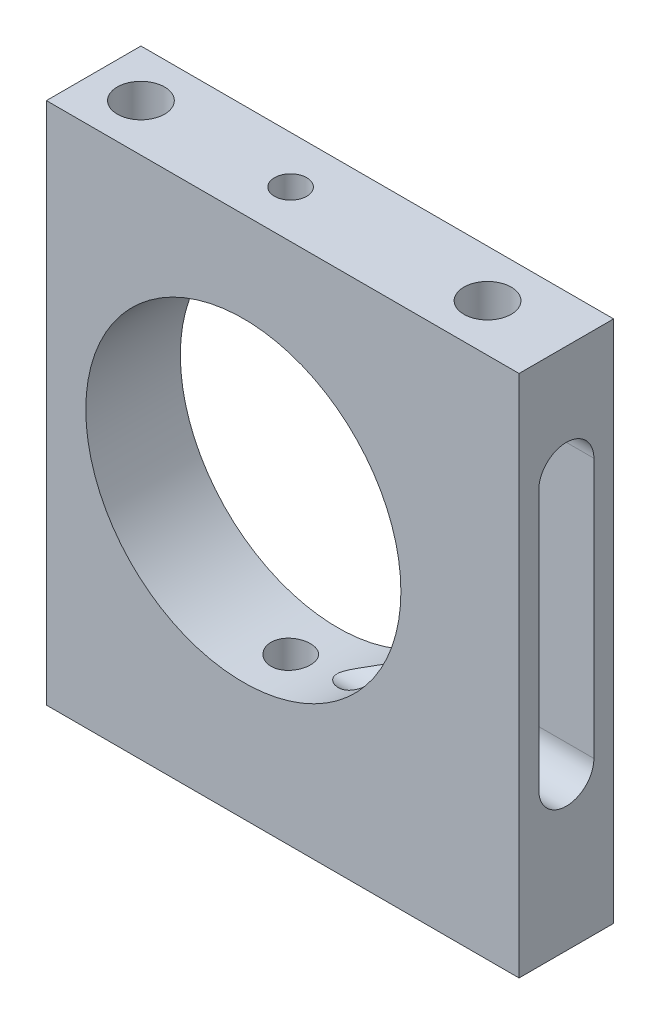
SolidWorks part; units mm, degrees
material "6061-T6 (SS)"
ref_plane "Front Plane" through (0, 0, 0) normal (0, 0, 1) x (1, 0, 0)
ref_plane "Top Plane" through (0, 0, 0) normal (0, 1, 0) x (1, 0, 0)
ref_plane "Right Plane" through (0, 0, 0) normal (1, 0, 0) x (0, 0, -1)
sketch "Sketch1" plane through (0, 0, 0) normal (0, 0, 1) x (1, 0, 0)
  line L1 (-17.5, -17.5) -> (17.5, -17.5)
  line L2 (-17.5, -17.5) -> (-17.5, 15.73)
  line L3 (-17.5, 15.73) -> (17.5, 15.73)
  line L4 (17.5, -17.5) -> (17.5, 15.73)
  line L5 (-17.5, -17.5) -> (0, 0) construction
  line L6 (0, 0) -> (17.5, -17.5) construction
  circle A0 centre (0, 0) radius 10
  point P0 (0, 0)
  dimension "D3" = 20
  dimension "D1" = 35
  dimension "D2" = 15.73
  dimension "D4" = 17.5
extrude "Boss-Extrude1" add sketch "Sketch1" along normal blind 6
sketch "Sketch2" plane through (17.5, 0, 0) normal (1, 0, 0) x (0, 0, -1)
  line L0 (-3, 15.73) -> (-3, -16.6121) construction
  line L1 (-6, 15.73) -> (0, 15.73) construction
  line L2 (-6.0882, -0.4411) -> (0.0882, -0.4411) construction
  line L5 (-4.75, -7.8061) -> (-4.75, 8.6939)
  line L7 (-1.25, -7.8061) -> (-1.25, 8.6939)
  arc A0 (-1.25, 8.6939) -> (-4.75, 8.6939) centre (-3, 8.6939) ccw
  arc A1 (-4.75, -7.8061) -> (-1.25, -7.8061) centre (-3, -7.8061) ccw
  point P6 (-3, -0.4411)
  point P12 (-3, -0.4411)
  dimension "D4" = 1.75
  dimension "D3" = 3.5
extrude "Cut-Extrude1" cut sketch "Sketch2" against normal blind 16
sketch "Sketch3" plane through (0, -17.5, 0) normal (0, -1, 0) x (1, 0, 0)
  line L0 (0, 4.6396) -> (0, 2.8092) construction
  line L1 (-2.1194, 3) -> (1.9267, 3) construction
  line L2 (17.5, 0) -> (-17.5, 0) construction
  dimension "D1" = 3
sketch "Sketch6" plane through (0, 15.73, 0) normal (0, 1, 0) x (1, 0, 0)
  line L0 (-14.9319, -3) -> (14.8838, -3) construction
  line L1 (-9.5, -2.1937) -> (-9.5, -5.6136) construction
  line L2 (12.5, -2.5791) -> (12.5, -5.6136) construction
  line L4 (17.5, -6) -> (17.5, 0) construction
  line L5 (17.5, 0) -> (-17.5, 0) construction
  dimension "D1" = 3
  dimension "D2" = 5
  dimension "D3" = 22
hole_wizard "Ø3.0mm Dowel Hole1" positions "Sketch7" profile "Sketch8" hole size "Ø3.0" standard "ANSI Metric"
sketch "Sketch7" plane through (0, 15.73, 0) normal (0, 1, 0) x (1, 0, 0)
  line L0 (-14.9319, -3) -> (14.8838, -3) construction
  line L1 (-9.5, -2.1937) -> (-9.5, -5.6136) construction
  line L2 (12.5, -2.5791) -> (12.5, -5.6136) construction
  point P0 (-9.5, -3)
  point P6 (12.5, -3)
sketch "Sketch8" plane through (-9.5, 15.73, 3) normal (1, 0, 0) x (0, 0, 1)
  line L0 (0, 0) -> (0, 8.1013)
  line L1 (0, 8.1013) -> (1.5, 7.2)
  line L2 (1.5, 7.2) -> (1.5, 0)
  line L5 (1.5, 0) -> (0, 0)
  line L10 (0, 8.1013) -> (-1.5, 7.2) construction
  line L11 (0, -6.35) -> (0, 107.95) construction
  dimension "Hole Dia." = 3
  dimension "Hole Depth" = 7.2
  dimension "Drill Angle" = 118
sketch "Sketch9" plane through (-17.5, 0, 0) normal (-1, 0, 0) x (0, 0, 1)
  line L1 (6, 15.73) -> (0, 15.73)
  line L2 (6, 15.73) -> (6, -17.5)
  line L3 (6, -17.5) -> (0, -17.5)
  line L4 (0, 15.73) -> (0, -17.5)
  line L5 (6, 15.73) -> (0, -17.5) construction
  line L6 (6, -17.5) -> (0, 15.73) construction
  point P4 (3, -0.885)
extrude "Cut-Extrude2" cut sketch "Sketch9" against normal blind 5
hole_wizard "M2.5x0.45 Tapped Hole1" positions "Sketch10" profile "Sketch11" tap size "M2.5x0.45" standard "ANSI Metric"
sketch "Sketch10" plane through (0, 15.73, 0) normal (0, 1, 0) x (1, 0, 0)
  line L0 (0, -4.6396) -> (0, -2.8092) construction
  line L1 (-2.1194, -3) -> (1.9267, -3) construction
  point P0 (0, -3)
sketch "Sketch11" plane through (0, 15.73, 3) normal (1, 0, 0) x (0, 0, 1)
  line L0 (0, 0) -> (0, 5.73)
  line L1 (0, 5.73) -> (1.025, 5.73)
  line L2 (1.025, 5.73) -> (1.025, 0)
  line L5 (1.025, 0) -> (0, 0)
  line L11 (0, -6.35) -> (0, 107.95) construction
  dimension "Thru Tap Drill Dia." = 2.05
  dimension "Thru Tap Drill Depth" = 5.73
cosmetic thread "Hole Thread1" parameters "D2"=2.5
hole_wizard "M3x0.5 Tapped Hole2" positions "Sketch14" profile "Sketch15" tap size "M3x0.5" standard "ANSI Metric"
sketch "Sketch14" plane through (0, -17.5, 0) normal (0, -1, 0) x (-1, 0, 0)
  point P0 (0, -2.9904)
sketch "Sketch15" plane through (0, -17.5, 2.9904) normal (1, 0, 0) x (0, 0, -1)
  line L0 (0, 0) -> (0, 7.5)
  line L1 (0, 7.5) -> (1.25, 7.5)
  line L2 (1.25, 7.5) -> (1.25, 0)
  line L5 (1.25, 0) -> (0, 0)
  line L11 (0, -6.35) -> (0, 107.95) construction
  dimension "Thru Tap Drill Dia." = 2.5
  dimension "Thru Tap Drill Depth" = 7.5
cosmetic thread "Hole Thread3" parameters "D2"=3
